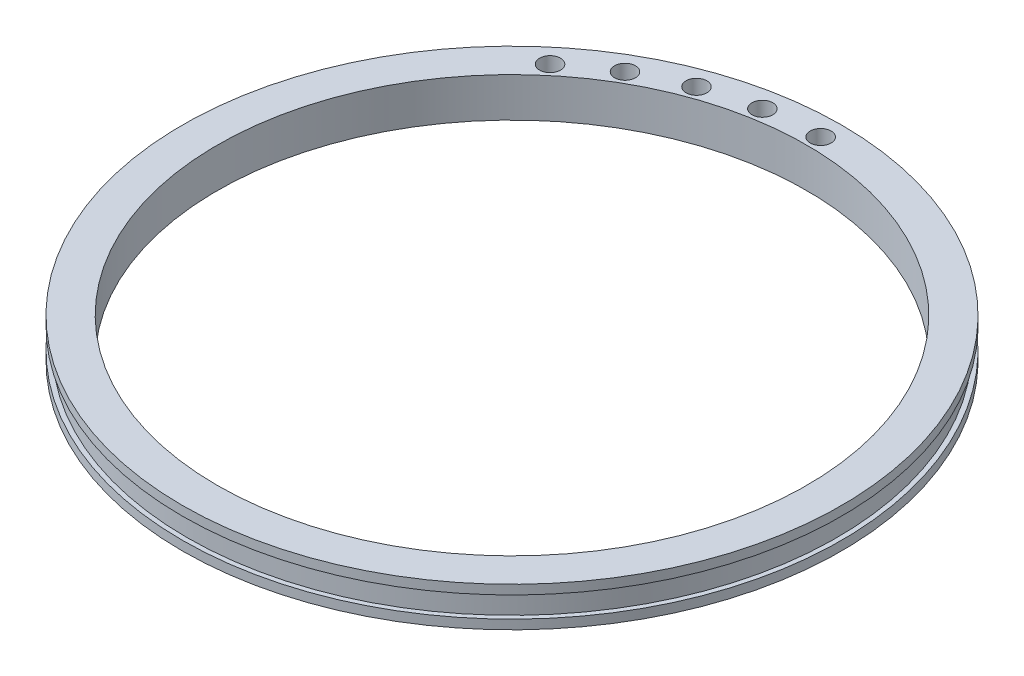
SolidWorks part; units mm, degrees
ref_plane "Front Plane" through (0, 0, 0) normal (0, 0, 1) x (1, 0, 0)
ref_plane "Top Plane" through (0, 0, 0) normal (0, 1, 0) x (1, 0, 0)
ref_plane "Right Plane" through (0, 0, 0) normal (1, 0, 0) x (0, 0, -1)
sketch "Sketch1" plane through (0, 0, 0) normal (0, 1, 0) x (1, 0, 0)
  circle A0 centre (0, 0) radius 70
  dimension "D1" = 140
extrude "Boss-Extrude1" add sketch "Sketch1" along normal mid plane 4.5
sketch "Sketch2" plane through (0, 2.25, 0) normal (0, 1, 0) x (1, 0, 0)
  circle A0 centre (0, 0) radius 71
  dimension "D1" = 142
extrude "Boss-Extrude2" add sketch "Sketch2" along normal blind 2
mirror "Mirror1" about plane through (0, 0, 0) normal (0, 1, 0) of "Boss-Extrude2"
sketch "Sketch3" plane through (0, 4.25, 0) normal (0, 1, 0) x (1, 0, 0)
  circle A0 centre (0, 0) radius 63.5
  dimension "D1" = 127
extrude "Cut-Extrude1" cut sketch "Sketch3" against normal through all both and the other way through all
sketch "Sketch5" plane through (0, 0, 0) normal (0, 1, 0) x (1, 0, 0)
  circle A0 centre (0, 0) radius 66.5 construction
  circle A1 centre (0, 66.5) radius 2.25
  dimension "D1" = 133
  dimension "D2" = 4.5
extrude "Cut-Extrude3" cut sketch "Sketch5" against normal through all both and the other way through all contours A1
pattern_circular "CirPattern1" count 5 every 10 about axis through (0, 0, 0) along (0, 1, 0) of "Cut-Extrude3"
